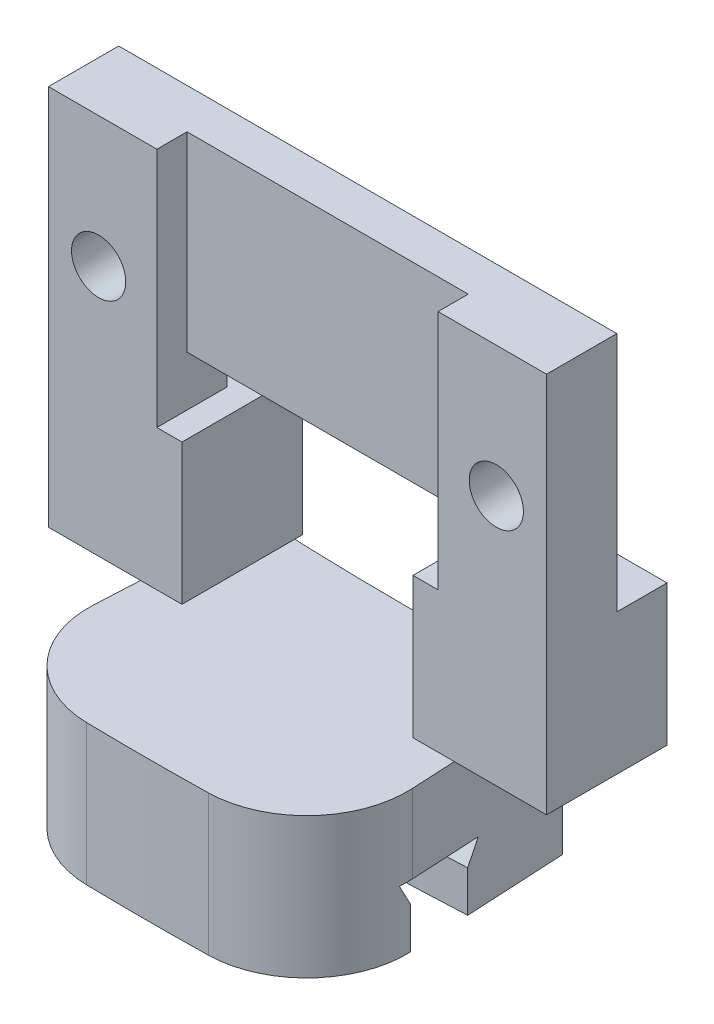
SolidWorks part; units mm, degrees
ref_plane "Front Plane" through (0, 0, 0) normal (0, 0, 1) x (1, 0, 0)
ref_plane "Top Plane" through (0, 0, 0) normal (0, 1, 0) x (1, 0, 0)
ref_plane "Right Plane" through (0, 0, 0) normal (1, 0, 0) x (0, 0, -1)
ref_axis "Axis2" through (0, 11, 0) along (0, -1, 0)
ref_plane "Plane2" through (0, 0, 143) normal (0, 0, 1) x (1, 0, 0)
sketch "Sketch7" plane through (0, 0, 143) normal (0, 0, 1) x (1, 0, 0)
  line L0 (-12.4, 0) -> (-5.75, 0)
  line L1 (-12.4, 19) -> (12.4, 19)
  line L2 (-12.4, 19) -> (-12.4, 0)
  line L3 (-5.75, 0) -> (-5.75, 7)
  line L4 (12.4, 19) -> (12.4, 0)
  line L5 (-5.75, 7) -> (5.75, 7)
  line L6 (5.75, 7) -> (5.75, 0)
  line L7 (5.75, 0) -> (12.4, 0)
  point P4 (0, -5)
  point P5 (14.3512, -0.3409)
  point P6 (12.4, 0)
  point P11 (0, 19)
  dimension "D1" = 24.8
  dimension "D2" = 7
  dimension "D3" = 11.5
  dimension "D5" = 12
extrude "Main" add sketch "Sketch7" along normal blind 6
sketch "Sketch8" plane through (0, 0, 149) normal (0, 0, 1) x (1, 0, 0)
  line L0 (12.4, 19) -> (-12.4, 19) construction
  line L1 (-12.4, 19) -> (-12.4, 0) construction
  circle A0 centre (-9.9, 12.5) radius 1.35
  circle A1 centre (9.9, 12.5) radius 1.35
  dimension "D1" = 2.7
  dimension "D2" = 19.8
  dimension "D3" = 6.5
  dimension "D4" = 2.5
extrude "Holes" cut sketch "Sketch8" against normal through all
sketch "Sketch9" plane through (0, 0, 149) normal (0, 0, 1) x (1, 0, 0)
  line L1 (12.4, 19) -> (-12.4, 19)
  line L2 (12.4, 19) -> (12.4, 7)
  line L3 (12.4, 7) -> (-12.4, 7)
  line L4 (-12.4, 19) -> (-12.4, 7)
  dimension "D3" = 12
sketch "Sketch12" plane through (0, 0, 149) normal (0, 0, 1) x (1, 0, 0)
  line L1 (-7, 19) -> (7, 19)
  line L2 (-7, 19) -> (-7, 7)
  line L3 (-7, 7) -> (7, 7)
  line L4 (7, 19) -> (7, 7)
  line L10 (12.4, 7) -> (-12.4, 7) construction
  line L12 (-12.4, 19) -> (-12.4, 7) construction
  line L13 (12.4, 19) -> (12.4, 7) construction
  dimension "D1" = 5.4
  dimension "D2" = 5.4
extrude "ComponentHoles2" cut sketch "Sketch12" against normal blind 1.5
sketch "Sketch17" plane through (0, 0, 147.5) normal (0, 0, 1) x (1, 0, 0)
  line L0 (7, 7) -> (7, 19) construction
  line L1 (-7, 7) -> (7, 7)
  line L2 (-7, 7) -> (-7, 9.5)
  line L3 (-7, 9.5) -> (7, 9.5)
  line L4 (7, 7) -> (7, 9.5)
  dimension "D1" = 2.5
extrude "HolesCables" cut sketch "Sketch17" against normal through all
sketch "Sketch16" plane through (12.4, 0, 0) normal (1, 0, 0) x (0, 0, -1)
  line L1 (-145.5, 19) -> (-143, 19)
  line L2 (-145.5, 19) -> (-145.5, 7)
  line L3 (-145.5, 7) -> (-143, 7)
  line L4 (-143, 19) -> (-143, 7)
  line L5 (-143, 0) -> (-143, 19) construction
  line L7 (-149, 7) -> (-143, 7) construction
  dimension "D1" = 2.5
extrude "FixExtrusion" cut sketch "Sketch16" against normal through all
sketch "Sketch10" plane through (0, 0, 0) normal (1, 0, 0) x (0, 0, -1)
  line L0 (-147.95, -3.9) -> (-152.05, -3.9)
  line L1 (-147.95, -3.9) -> (-148.5, -4.95)
  line L2 (-148.5, -4.95) -> (-148.5, -7)
  line L3 (-148.5, -7) -> (-143.5, -7)
  line L4 (-143.5, -7) -> (-143.5, 0)
  line L5 (-143.5, 0) -> (-156.5, 0)
  line L6 (-156.5, 0) -> (-156.5, -7)
  line L7 (-152.05, -3.9) -> (-151.5, -4.95)
  line L8 (-151.5, -4.95) -> (-151.5, -7)
  line L9 (-151.5, -7) -> (-156.5, -7)
  line L11 (-149, 0) -> (-143, 0) construction
  point P9 (-150, 0)
  point P12 (-150, -3.9)
  dimension "D1" = 3
  dimension "D2" = 5
  dimension "D3" = 4.1
  dimension "D4" = 2.05
  dimension "D5" = 3.1
  dimension "D6" = 7
  dimension "D7" = 150
  dimension "D9" = 5
revolve "Support" add sketch "Sketch10" angle 6 mid plane about axis through (0, 11, 0) along (0, -1, 0)
fillet "Fillet1" radius 5 2 edges at (8.1906, -3.5, 156.2855) (-8.1906, -3.5, 156.2855)
